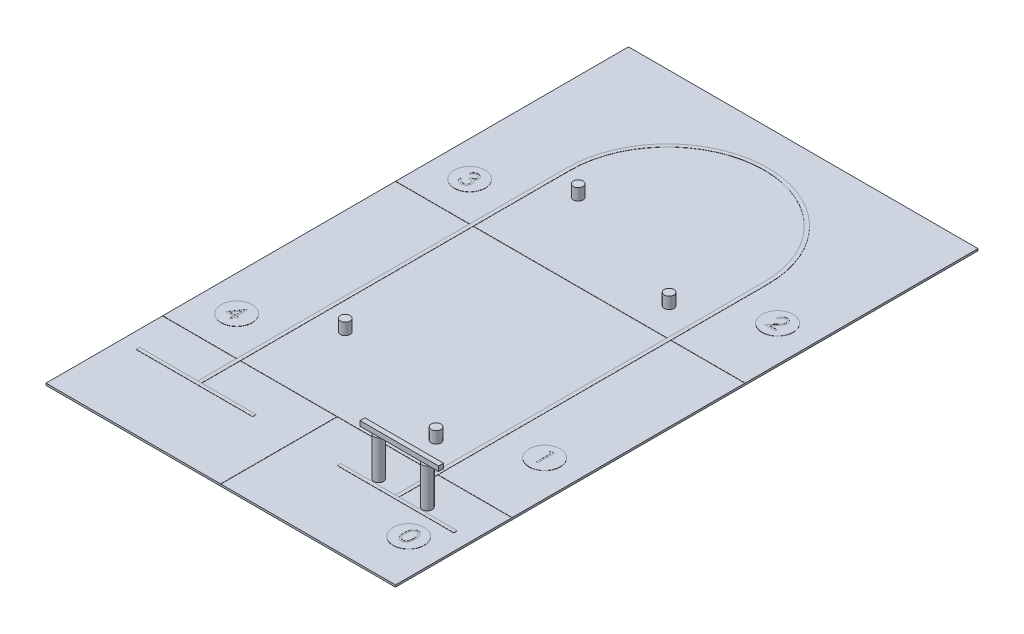
SolidWorks part; units mm, degrees
ref_plane "Front" through (0, 0, 0) normal (0, 0, 1) x (1, 0, 0)
ref_plane "Top" through (0, 0, 0) normal (0, 1, 0) x (1, 0, 0)
ref_plane "Right" through (0, 0, 0) normal (1, 0, 0) x (0, 0, -1)
sketch "草圖1" plane through (0, 0, 0) normal (0, 1, 0) x (1, 0, 0)
  line L0 (500, 0) -> (500, 1900)
  line L1 (-500, 1900) -> (-500, 0)
  line L2 (-500, 0) -> (500, 0) construction
  arc A0 (500, 1900) -> (-500, 1900) centre (0, 1900) ccw
  dimension "D3" = 500
  dimension "D1" = 1900
  dimension "D2" = 1900
extrude "伸長-薄件1" add sketch "草圖1" along normal blind 1 thin
sketch "草圖2" plane through (0, 0, 0) normal (0, -1, 0) x (-1, 0, 0)
  line L0 (0, 200) -> (0, -400) construction
  line L1 (-900, -400) -> (900, -400)
  line L2 (-900, -400) -> (-900, 2600)
  line L3 (-900, 2600) -> (900, 2600)
  line L4 (900, -400) -> (900, 2600)
  line L5 (-518, 0) -> (-518, 1900) construction
  line L6 (900, 200) -> (-900, 200) construction
  line L7 (900, 1400) -> (-900, 1400) construction
  line L8 (518, 1900) -> (518, 0) construction
  dimension "D1" = 3000
  dimension "D2" = 1800
  dimension "D3" = 400
  dimension "D4" = 382
  dimension "D5" = 382
  dimension "D7" = 1200
  dimension "D10" = 1200
  dimension "D13" = 600
extrude "填料-伸長1" add sketch "草圖2" along normal blind 10 separate body
sketch "草圖3" plane through (0, 0, 0) normal (0, 1, 0) x (1, 0, 0)
  line L0 (818, 0) -> (218, 0)
  line L1 (-218, 0) -> (-818, 0)
  line L6 (518, 0) -> (518, 1900) construction
  line L7 (-518, 1900) -> (-518, 0) construction
  dimension "D1" = 600
  dimension "D2" = 600
  dimension "D3" = 300
  dimension "D4" = 300
extrude "伸長-薄件2" add sketch "草圖3" along normal blind 1 separate body thin thin type one direction reverse wall 18
sketch "草圖4" plane through (0, 0, 0) normal (0, 1, 0) x (1, 0, 0)
  line L0 (0, 828) -> (0, 0) construction
  line L2 (-718, 1600) -> (-718, 400) construction
  line L4 (718, 1750) -> (718, 550) construction
  line L5 (518, 0) -> (518, 1900) construction
  line L6 (-518, 1900) -> (-518, 0) construction
  line L7 (-900, 2600) -> (900, 2600) construction
  line L8 (900, -400) -> (-900, -400) construction
  line L9 (718, 550) -> (718, -150) construction
  circle A0 centre (718, 550) radius 80
  circle A2 centre (718, 1750) radius 80
  circle A3 centre (-718, 1600) radius 80
  circle A4 centre (-718, 400) radius 80
  circle A5 centre (718, -150) radius 80
  dimension "D1" = 160
  dimension "D5" = 1000
  dimension "D7" = 250
  dimension "D9" = 700
  dimension "D2" = 200
  dimension "D3" = 200
  dimension "D6" = 1200
  dimension "D8" = 1200
extrude "填料-伸長2" add sketch "草圖4" along normal blind 1 separate body
sketch "草圖5" plane through (0, 1, 0) normal (0, 1, 0) x (1, 0, 0)
  text T0 "1" font "Century Gothic" height in points 300
  text T1 "2" font "Century Gothic" height in points 300
  text T2 "3" font "Century Gothic" height in points 300
  text T3 "4" font "Century Gothic" height in points 300
  text T4 "0\r\n" font "Century Gothic" height in points 300
extrude "除料-伸長1" cut sketch "草圖5" against normal blind 0.5
sketch "草圖6" plane through (0, 0, 0) normal (0, 1, 0) x (1, 0, 0)
  line L0 (359, 1550) -> (359, 350) construction
  line L1 (-359, 1800) -> (-359, 600) construction
  line L2 (499, 0) -> (499, 1900) construction
  line L3 (-499, 1900) -> (-499, 0) construction
  line L4 (518, 0) -> (518, 1900) construction
  line L5 (818, 0) -> (218, 0) construction
  circle A0 centre (359, 350) radius 25
  circle A1 centre (359, 1550) radius 25
  circle A2 centre (-359, 1800) radius 25
  circle A3 centre (-359, 600) radius 25
  circle A4 centre (383, 30) radius 25 construction
  circle A5 centre (634, 30) radius 25 construction
  circle A6 centre (-718, 400) radius 80 construction
  circle A8 centre (-718, 1600) radius 80 construction
  circle A9 centre (718, 1750) radius 80 construction
  circle A10 centre (718, 550) radius 80 construction
  dimension "D1" = 50
  dimension "D4" = 116
  dimension "D5" = 116
  dimension "D6" = 30
  dimension "D7" = 30
  dimension "D8" = 200
  dimension "D9" = 200
  dimension "D10" = 200
  dimension "D11" = 200
  dimension "D2" = 140
  dimension "D3" = 140
extrude "填料-伸長3" add sketch "草圖6" along normal blind 60 separate body
sketch "草圖8" plane through (0, 0, 0) normal (0, 1, 0) x (1, 0, 0)
  circle A0 centre (383, 30) radius 24.9909
  circle A1 centre (634, 30) radius 25.2108
extrude "填料-伸長5" add sketch "草圖8" along normal blind 200 separate body
sketch "草圖7" plane through (0, 200, 0) normal (0, 1, 0) x (1, 0, 0)
  line L1 (300.8538, 41.5541) -> (705.3156, 41.5541)
  line L2 (300.8538, 41.5541) -> (300.8538, 16.5541)
  line L3 (300.8538, 16.5541) -> (705.3156, 16.5541)
  line L4 (705.3156, 41.5541) -> (705.3156, 16.5541)
  dimension "D1" = 25
extrude "填料-伸長4" add sketch "草圖7" along normal blind 25
sketch "草圖9" plane through (0, 0, 0) normal (0, 1, 0) x (1, 0, 0)
  line L0 (-900, 2600) -> (900, 2600) construction
  line L2 (-900, 1400) -> (900, 1400)
  line L3 (-900, -400) -> (-900, 2600) construction
  line L4 (900, 2600) -> (900, -400) construction
  line L5 (-900, 200) -> (900, 200)
  dimension "D1" = 1200
  dimension "D2" = 1200
extrude "除料-伸長-薄件1" cut sketch "草圖9" against normal blind 1 thin thin type two direction wall 1 second wall 1
sketch "草圖10" plane through (0, 0, 0) normal (0, 1, 0) x (1, 0, 0)
  line L0 (0, 199) -> (0, -400)
  line L1 (-900, 199) -> (900, 199) construction
  line L2 (900, -400) -> (-900, -400) construction
extrude "除料-伸長-薄件2" cut sketch "草圖10" against normal blind 1 thin thin type two direction wall 1 second wall 1
